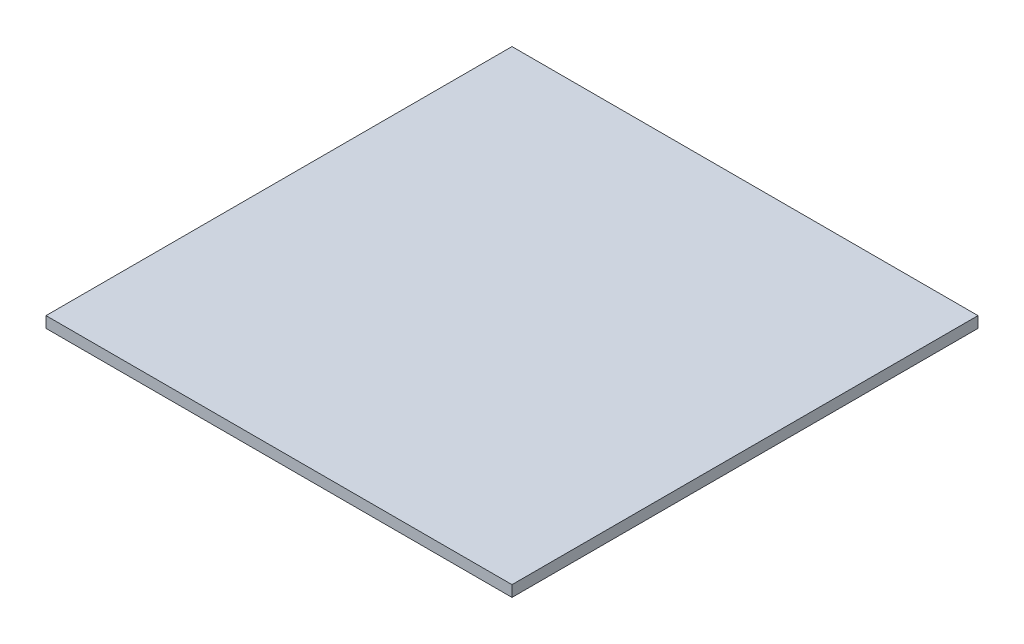
SolidWorks part; units mm, degrees
ref_plane "Plan de face" through (0, 0, 0) normal (0, 0, 1) x (1, 0, 0)
ref_plane "Plan de dessus" through (0, 0, 0) normal (0, 1, 0) x (1, 0, 0)
ref_plane "Plan de droite" through (0, 0, 0) normal (1, 0, 0) x (0, 0, -1)
sketch "Esquisse1" plane through (0, 0, 0) normal (0, 1, 0) x (1, 0, 0)
  line L1 (0, 0) -> (420, 0)
  line L2 (0, 0) -> (0, 420)
  line L3 (0, 420) -> (420, 420)
  line L4 (420, 0) -> (420, 420)
  dimension "D1" = 420
  dimension "D2" = 420
extrude "Boss.-Extru.1" add sketch "Esquisse1" along normal blind 10
